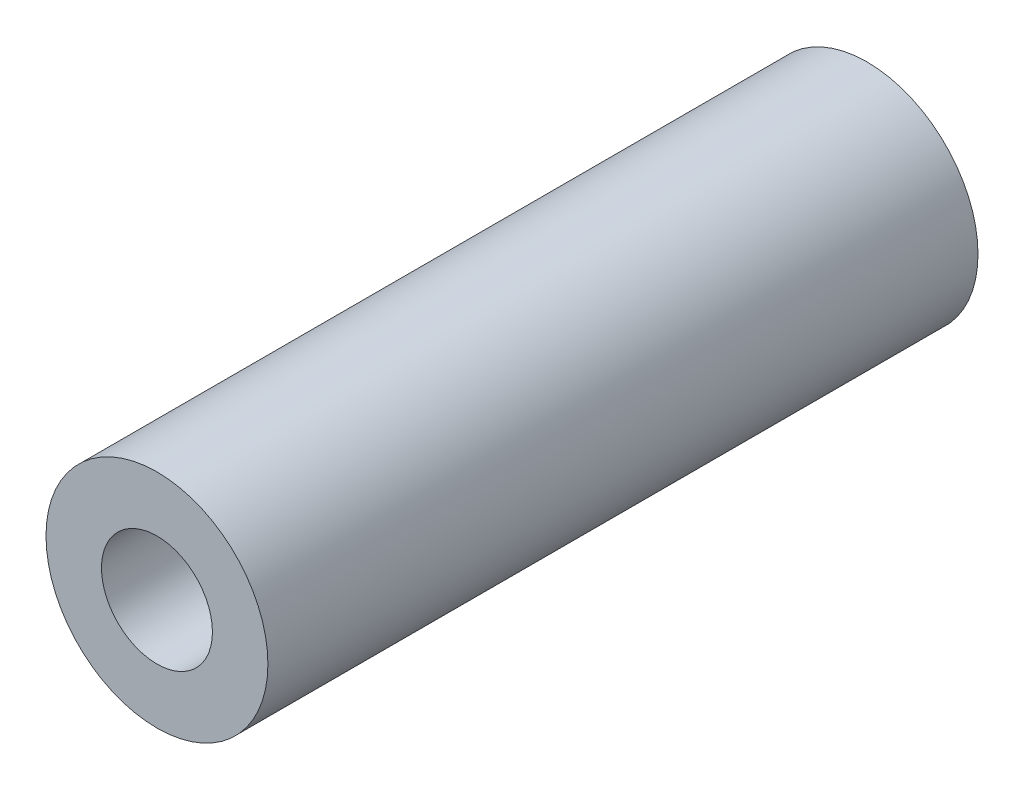
SolidWorks part; units mm, degrees
ref_plane "Plan de face" through (0, 0, 0) normal (0, 0, 1) x (1, 0, 0)
ref_plane "Plan de dessus" through (0, 0, 0) normal (0, 1, 0) x (1, 0, 0)
ref_plane "Plan de droite" through (0, 0, 0) normal (1, 0, 0) x (0, 0, -1)
sketch "Esquisse1" plane through (0, 0, 0) normal (0, 0, 1) x (1, 0, 0)
  circle A0 centre (0, 0) radius 1.25
  circle A1 centre (0, 0) radius 2.5
  dimension "D1" = 2.5
  dimension "D2" = 5
extrude "Boss.-Extru.1" add sketch "Esquisse1" along normal blind 16
